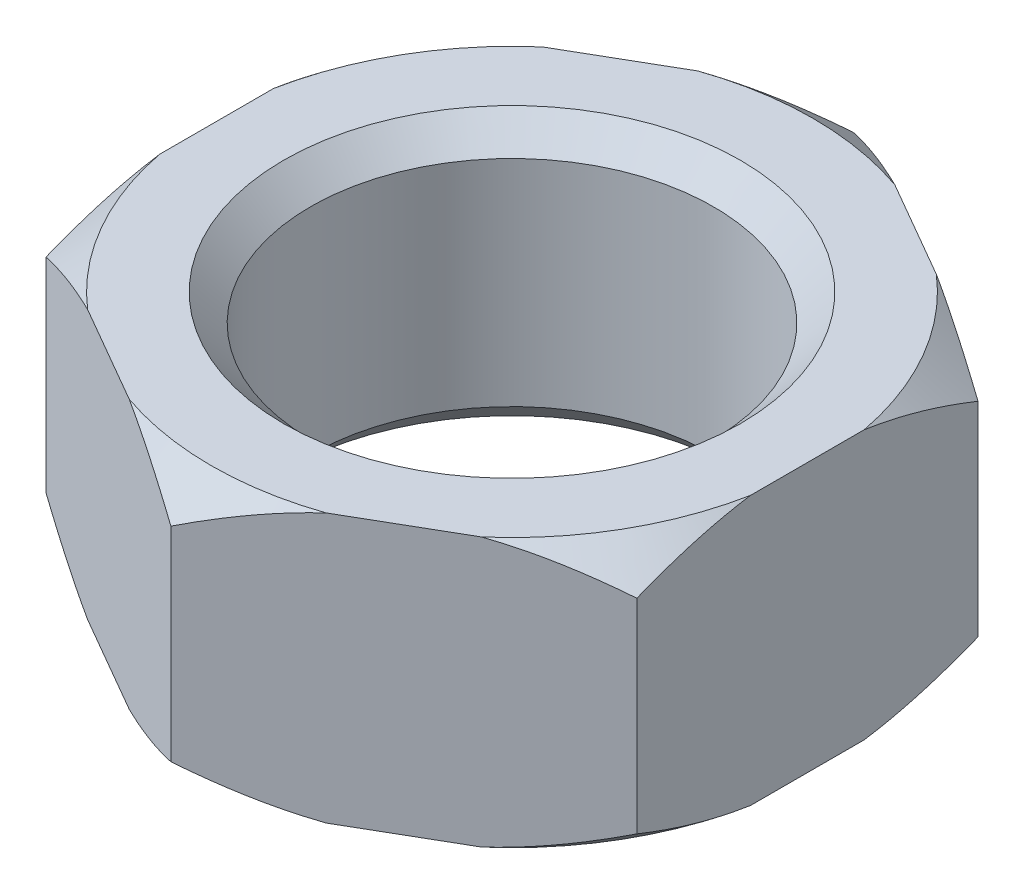
SolidWorks part; units mm, degrees
material "AISI 316 Stainless Steel Sheet (SS)"
ref_plane "Front Plane" through (0, 0, 0) normal (0, 0, 1) x (1, 0, 0)
ref_plane "Top Plane" through (0, 0, 0) normal (0, 1, 0) x (1, 0, 0)
ref_plane "Right Plane" through (0, 0, 0) normal (1, 0, 0) x (0, 0, -1)
sketch "Sketch1" plane through (0, 0, 0) normal (0, 1, 0) x (1, 0, 0)
  line L1 (0, 12.7017) -> (-11, 6.3509)
  line L2 (-11, 6.3509) -> (-11, -6.3509)
  line L3 (-11, -6.3509) -> (0, -12.7017)
  line L4 (0, -12.7017) -> (11, -6.3509)
  line L5 (11, -6.3509) -> (11, 6.3509)
  line L6 (11, 6.3509) -> (0, 12.7017)
  circle A0 centre (0, 0) radius 11 construction
  dimension "D1" = 22
extrude "Boss-Extrude1" add sketch "Sketch1" along normal blind 10
sketch "Sketch2" plane through (0, 10, 0) normal (0, 1, 0) x (1, 0, 0)
  circle A0 centre (0, 0) radius 7.5
  dimension "D1" = 15
extrude "Cut-Extrude1" cut sketch "Sketch2" against normal through all
cosmetic thread "Cosmetic Thread1" parameters "D2"=24
chamfer "Chamfer1" distance 1 angle 45 2 edges at (0, 10, 7.5) (0, 0, 7.5)
sketch "Sketch3" plane through (0, 0, 0) normal (1, 0, 0) x (0, 0, -1)
  line L0 (0, 10) -> (0, 0) construction
  line L1 (-6.3509, 10) -> (6.3509, 10) construction
  line L2 (-12.7017, 10) -> (-12.7017, 8.8)
  line L3 (-12.7017, 10) -> (-12.7017, 0) construction
  line L4 (-12.7017, 8.8) -> (-11.2017, 10)
  line L5 (-12.7017, 10) -> (-6.3509, 10) construction
  line L6 (-11.2017, 10) -> (-12.7017, 10)
  line L7 (-12.7017, 0) -> (-12.7017, 1.2)
  line L8 (-12.7017, 1.2) -> (-11.2017, 0)
  line L9 (-12.7017, 0) -> (-6.3509, 0) construction
  line L10 (-11.2017, 0) -> (-12.7017, 0)
  dimension "D1" = 1.5
  dimension "D2" = 1.2
  dimension "D3" = 1.5
  dimension "D4" = 1.2
revolve "Cut-Revolve1" cut sketch "Sketch3" angle 360 about L0
scale "Scale2" scale about centroid uniform scaling yes scale factor 0.18
scale "Scale3" scale about centroid uniform scaling yes scale factor 1.04
